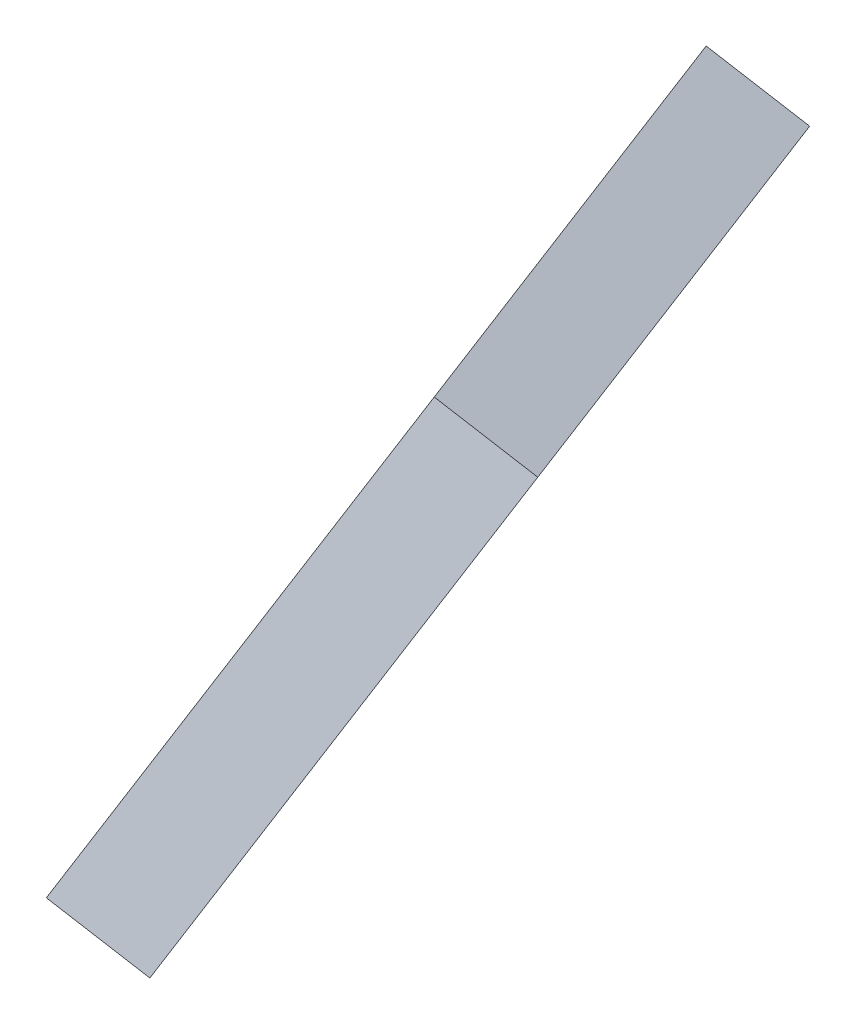
SolidWorks part; units mm, degrees
material "Beech"
ref_plane "Front Plane" through (0, 0, 0) normal (0, 0, 1) x (1, 0, 0)
ref_plane "Top Plane" through (0, 0, 0) normal (0, 1, 0) x (1, 0, 0)
ref_plane "Right Plane" through (0, 0, 0) normal (1, 0, 0) x (0, 0, -1)
sketch "Sketch2" plane through (-19.7966, 12.235, 7.5616) normal (0.809, -0.5, -0.309) x (-0.2629, 0.1625, -0.9511)
  line L0 (-40.5434, 50.1677) -> (-37.5967, 49.6049)
  line L1 (-37.5967, 49.6049) -> (-38.3744, 45.5326)
  line L2 (-38.3744, 45.5326) -> (-41.669, 43.0158)
  line L3 (-41.669, 43.0158) -> (-43.4902, 45.3998)
  line L4 (-51.4291, 53.6008) -> (-62.509, 45.1366) construction
  line L5 (-49.6079, 51.2169) -> (-60.6878, 42.7526) construction
  line L6 (-43.4902, 45.3998) -> (-51.4921, 39.2869)
  line L7 (-51.4921, 39.2869) -> (-60.4754, 50.6689)
  line L8 (-60.4754, 50.6689) -> (-52.8523, 63.0033)
  line L9 (-56.6638, 56.8361) -> (-38.3744, 45.5326) construction
  line L10 (-40.5434, 50.1677) -> (-43.4902, 45.3998) construction
  line L11 (-38.6545, 60.0586) -> (-52.8523, 63.0033)
  line L12 (-40.5434, 50.1677) -> (-38.6545, 60.0586)
  point P4 (-42.0168, 47.7837)
  dimension "D2" = 14.5
  dimension "D3" = 110
extrude "Boss-Extrude1" add sketch "Sketch2" along normal blind 2.8
equation "\"D1@Boss-Extrude1\"=\"T@d20.Assembly\"-0.2"
